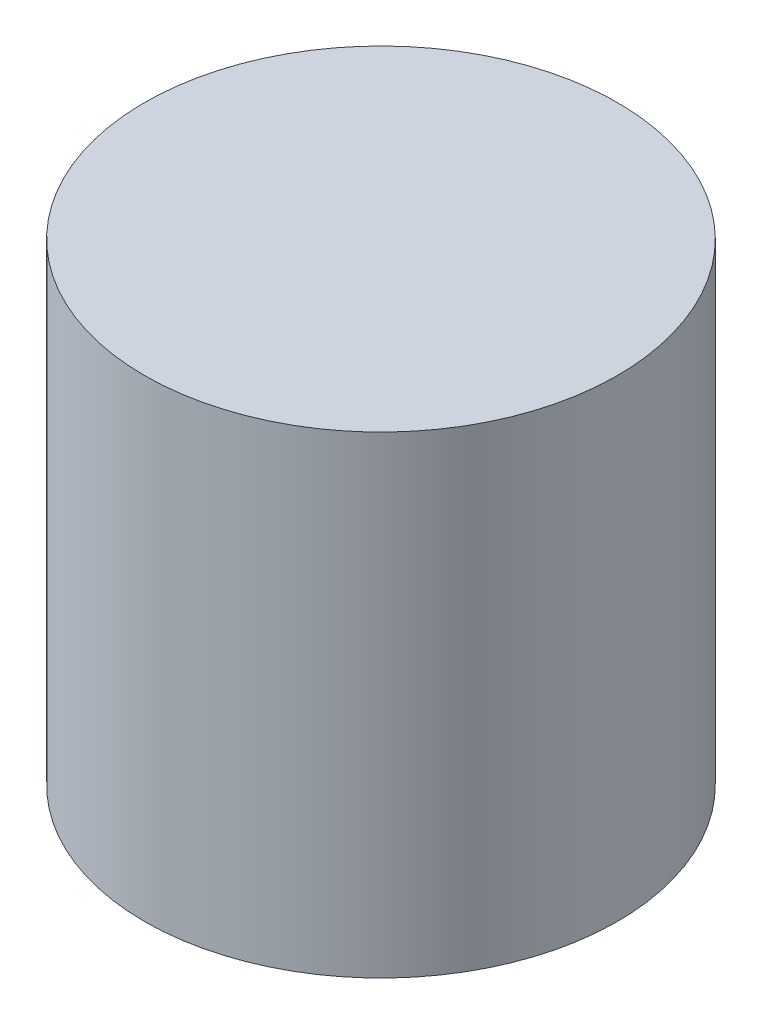
SolidWorks part; units mm, degrees
ref_plane "Front Plane" through (0, 0, 0) normal (0, 0, 1) x (1, 0, 0)
ref_plane "Top Plane" through (0, 0, 0) normal (0, 1, 0) x (1, 0, 0)
ref_plane "Right Plane" through (0, 0, 0) normal (1, 0, 0) x (0, 0, -1)
sketch "Sketch1" plane through (0, 0, 0) normal (0, 1, 0) x (1, 0, 0)
  circle A0 centre (-59.7494, 21.0516) radius 63.5
  dimension "D1" = 127
extrude "Boss-Extrude1" add sketch "Sketch1" along normal blind 127
